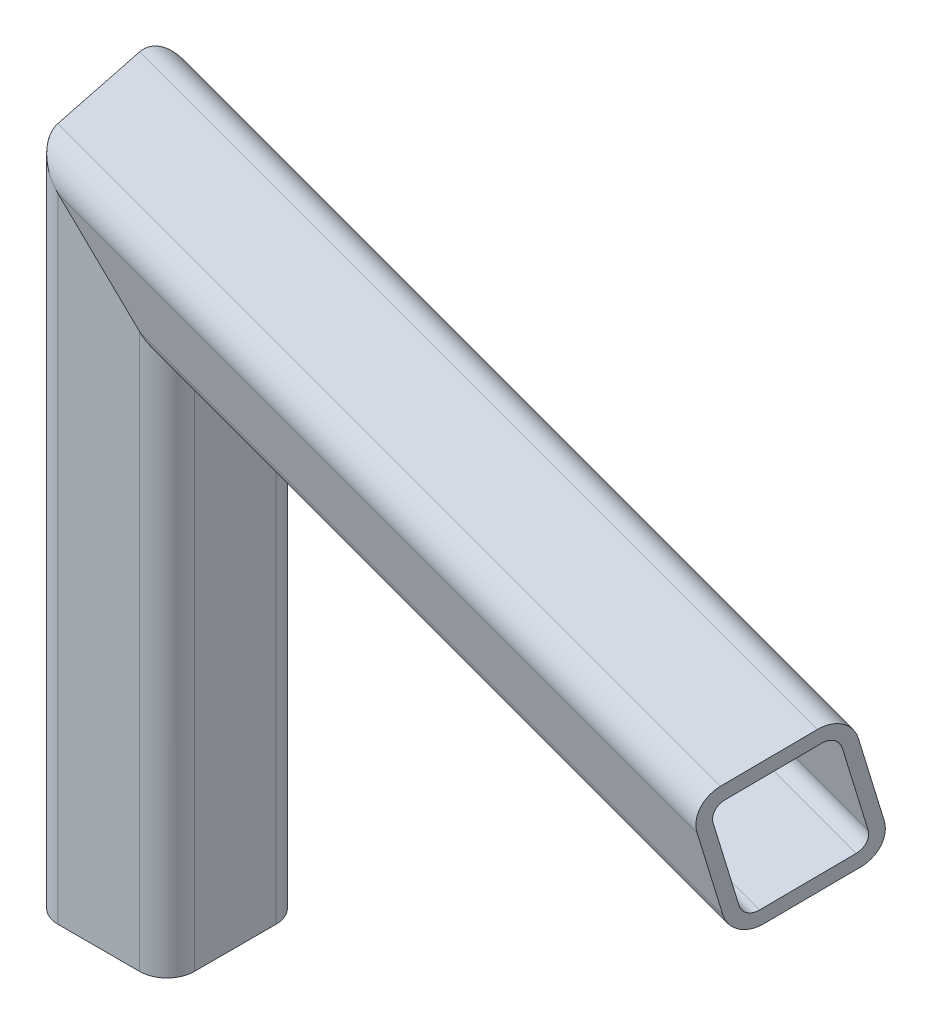
SolidWorks part; units mm, degrees
ref_plane "Ebene vorne" through (0, 0, 0) normal (0, 0, 1) x (1, 0, 0)
ref_plane "Ebene oben" through (0, 0, 0) normal (0, 1, 0) x (1, 0, 0)
ref_plane "Ebene rechts" through (0, 0, 0) normal (1, 0, 0) x (0, 0, -1)
sketch3d "3D-Skizze1"
  line L0 (0, 0, 0) -> (0, 89.6614, 0)
  line L1 (0, 89.6614, 0) -> (125, 89.6614, 33.4936)
  line L2 (125, 89.6614, 33.4936) -> (250, 89.6614, 0)
  line L3 (250, 89.6614, 0) -> (250, 0, 0)
  line L4 (125, 89.6614, 0) -> (125, 89.6614, 60.973) construction
  line L5 (0, 0, 0) -> (125, 0, 33.4936)
  line L6 (0, 89.6614, 0) -> (250, 89.6614, 0) construction
  line L7 (125, 0, 33.4936) -> (250, 0, 0)
  line L8 (0, 0, 0) -> (250, 0, 0) construction
  line L9 (125, 0, 0) -> (125, 0, 45.0159) construction
  dimension "D1" = 15
  dimension "D2" = 250
  dimension "D3" = 15
other "Quadratisches hohlprofil 20 X 20 X 2(24)"
ref_plane "Ebene5" through (0, 0, 0) normal (0, 1, 0) x (1, 0, 0)
sketch "Sketch1" plane through (0, 0, 0) normal (0, 1, 0) x (1, 0, 0)
  line L0 (-6, -8) -> (6, -8)
  line L1 (-8, -6) -> (-8, 6)
  line L2 (6, 8) -> (-6, 8)
  line L3 (8, 6) -> (8, -6)
  line L4 (-6, -10) -> (6, -10)
  line L5 (-10, -6) -> (-10, 6)
  line L6 (6, 10) -> (-6, 10)
  line L7 (10, 6) -> (10, -6)
  arc A0 (10, 6) -> (6, 10) centre (6, 6) ccw
  arc A1 (6, -10) -> (10, -6) centre (6, -6) ccw
  arc A2 (-10, -6) -> (-6, -10) centre (-6, -6) ccw
  arc A3 (-6, 10) -> (-10, 6) centre (-6, 6) ccw
  arc A4 (-6, 8) -> (-8, 6) centre (-6, 6) ccw
  arc A5 (8, 6) -> (6, 8) centre (6, 6) ccw
  arc A6 (6, -8) -> (8, -6) centre (6, -6) ccw
  arc A7 (-8, -6) -> (-6, -8) centre (-6, -6) ccw
  point P0 (-10, 0)
  point P1 (10, 0)
  point P2 (0, 10)
  point P3 (0, -10)
  point P4 (0, 0)
  point P5 (-10, -10)
  point P6 (10, -10)
  point P7 (10, 10)
  point P8 (-10, 10)
  point P33 (0, 0)
  dimension "D1" = 4
  dimension "Thickness" = 2
  dimension "V_leg" = 20
